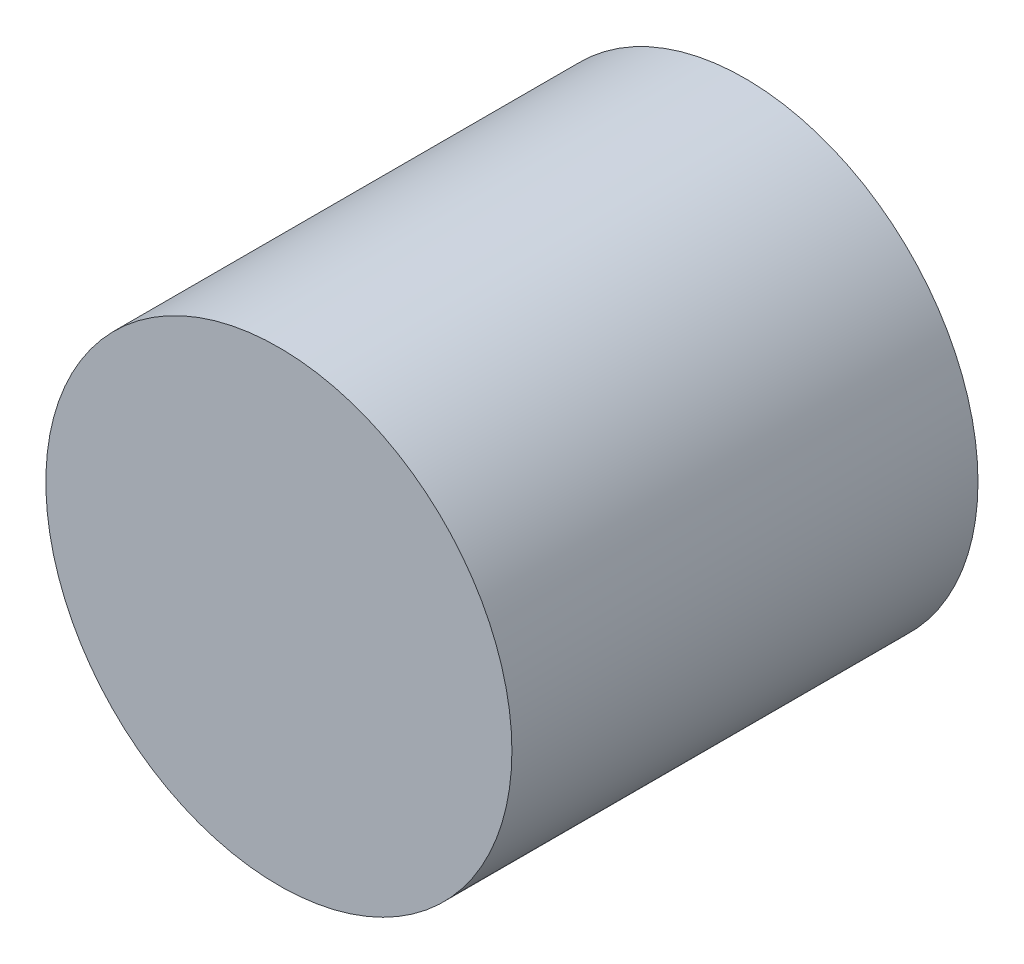
SolidWorks part; units mm, degrees
ref_plane "Front Plane" through (0, 0, 0) normal (0, 0, 1) x (1, 0, 0)
ref_plane "Top Plane" through (0, 0, 0) normal (0, 1, 0) x (1, 0, 0)
ref_plane "Right Plane" through (0, 0, 0) normal (1, 0, 0) x (0, 0, -1)
sketch "Sketch1" plane through (0, 0, 0) normal (0, 0, 1) x (1, 0, 0)
  circle A0 centre (0, 0) radius 12.5
  dimension "D1" = 25
extrude "Boss-Extrude1" add sketch "Sketch1" along normal blind 25
